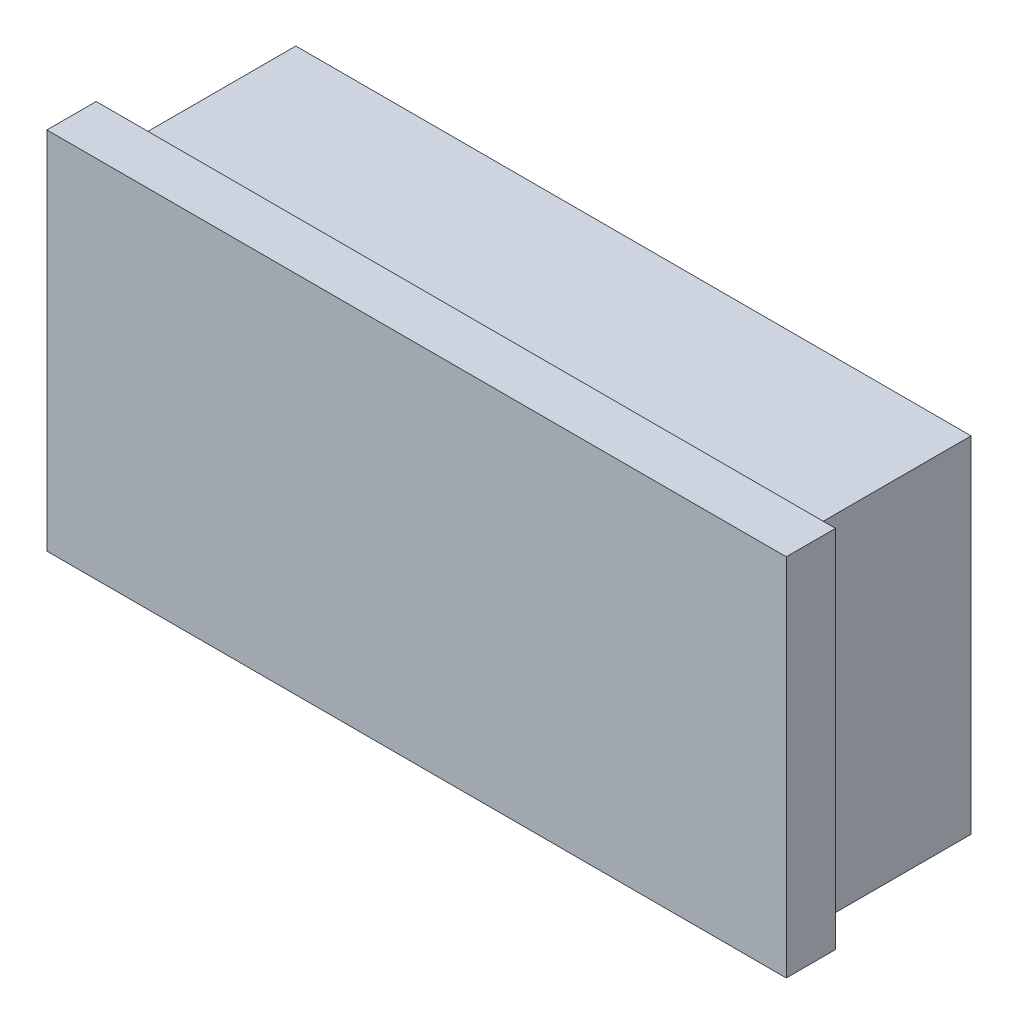
SolidWorks part; units mm, degrees
ref_plane "Plano frontal" through (0, 0, 0) normal (0, 0, 1) x (1, 0, 0)
ref_plane "Plano superior" through (0, 0, 0) normal (0, 1, 0) x (1, 0, 0)
ref_plane "Plano direito" through (0, 0, 0) normal (1, 0, 0) x (0, 0, -1)
sketch "Esboço1" plane through (0, 0, 0) normal (0, 0, 1) x (1, 0, 0)
  line L1 (0, 0) -> (548, 0)
  line L2 (0, 0) -> (0, 280)
  line L3 (0, 280) -> (548, 280)
  line L4 (548, 0) -> (548, 280)
  dimension "D1" = 548
  dimension "D2" = 280
extrude "Ressalto-extrusão1" add sketch "Esboço1" along normal blind 176
sketch "Esboço2" plane through (0, 0, 0) normal (-1, 0, 0) x (0, 0, 1)
  line L0 (176, 280) -> (0, 280) construction
  line L1 (176, 0) -> (136, 0)
  line L2 (176, 0) -> (176, 280)
  line L3 (176, 280) -> (136, 280)
  line L4 (136, 0) -> (136, 280)
  dimension "D1" = 40
extrude "Ressalto-extrusão2" add sketch "Esboço2" along normal blind 26
sketch "Esboço3" plane through (548, 0, 0) normal (1, 0, 0) x (0, 0, -1)
  line L0 (-176, 0) -> (0, 0) construction
  line L1 (-176, 280) -> (-136, 280)
  line L2 (-176, 280) -> (-176, 0)
  line L3 (-176, 0) -> (-136, 0)
  line L4 (-136, 280) -> (-136, 0)
  dimension "D1" = 40
extrude "Ressalto-extrusão3" add sketch "Esboço3" along normal blind 26
sketch "Esboço4" plane through (0, 280, 0) normal (0, 1, 0) x (1, 0, 0)
  line L1 (-26, -136) -> (574, -136)
  line L2 (-26, -136) -> (-26, -176)
  line L3 (-26, -176) -> (574, -176)
  line L4 (574, -136) -> (574, -176)
extrude "Ressalto-extrusão4" add sketch "Esboço4" along normal blind 16
